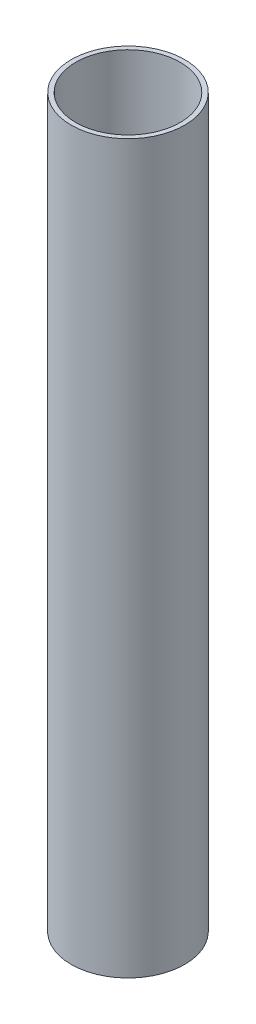
SolidWorks part; units mm, degrees
material "3.1355 (EN-AW 2024)"
ref_plane "Front" through (0, 0, 0) normal (0, 0, 1) x (1, 0, 0)
ref_plane "Top" through (0, 0, 0) normal (0, 1, 0) x (1, 0, 0)
ref_plane "Right" through (0, 0, 0) normal (1, 0, 0) x (0, 0, -1)
sketch "Эскиз1" plane through (0, 0, 0) normal (0, 1, 0) x (1, 0, 0)
  circle A0 centre (0, 0) radius 12.5
  circle A1 centre (0, 0) radius 11.5
  dimension "D1" = 25
  dimension "D2" = 23
extrude "Бобышка-Вытянуть1" add sketch "Эскиз1" along normal blind 160
